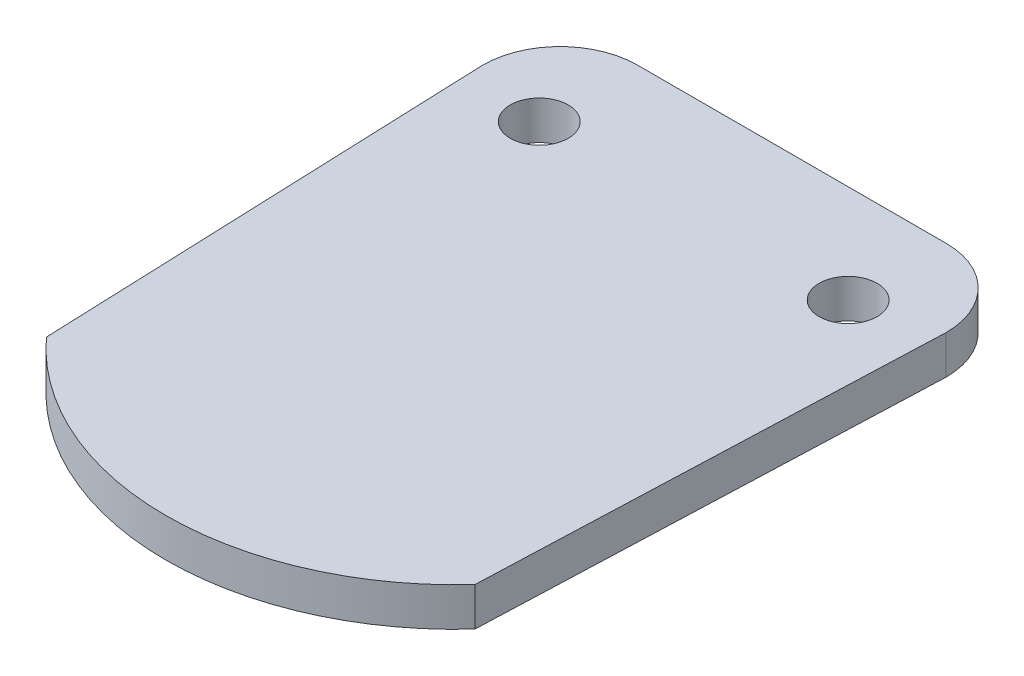
SolidWorks part; units mm, degrees
ref_plane "Front Plane" through (0, 0, 0) normal (0, 0, 1) x (1, 0, 0)
ref_plane "Top Plane" through (0, 0, 0) normal (0, 1, 0) x (1, 0, 0)
ref_plane "Right Plane" through (0, 0, 0) normal (1, 0, 0) x (0, 0, -1)
sketch "Sketch1" plane through (0, 0, 0) normal (0, 1, 0) x (1, 0, 0)
  line L1 (-13.2, 0) -> (13.2, 0) construction
  line L2 (0, -25.1858) -> (0, 25.1858) construction
  line L3 (0, 17.3726) -> (0, -15.4303) construction
  line L4 (-8, 4) -> (8, 4)
  line L5 (-12, 0) -> (-11.099, -23.51)
  line L6 (12, 0) -> (11.099, -23.51)
  arc A0 (-12, 0) -> (-8, 4) centre (-8, 0) cw
  arc A1 (12, 0) -> (8, 4) centre (8, 0) ccw
  arc A2 (-11.099, -23.51) -> (11.099, -23.51) centre (0, -13.4198) ccw
  circle A3 centre (-8, -1.08) radius 1.5
  circle A4 centre (8, -1.08) radius 1.5
  dimension "D2" = 4
  dimension "D3" = 4
  dimension "D6" = 15
  dimension "D8" = 3
  dimension "D9" = 3
  dimension "D1" = 24
  dimension "D4" = 16
  dimension "D5" = 23.51
  dimension "D7" = 22.198
  dimension "D10" = 5.08
  dimension "D11" = 5.08
  dimension "D12" = 16
extrude "Boss-Extrude1" add sketch "Sketch1" along normal blind 2
